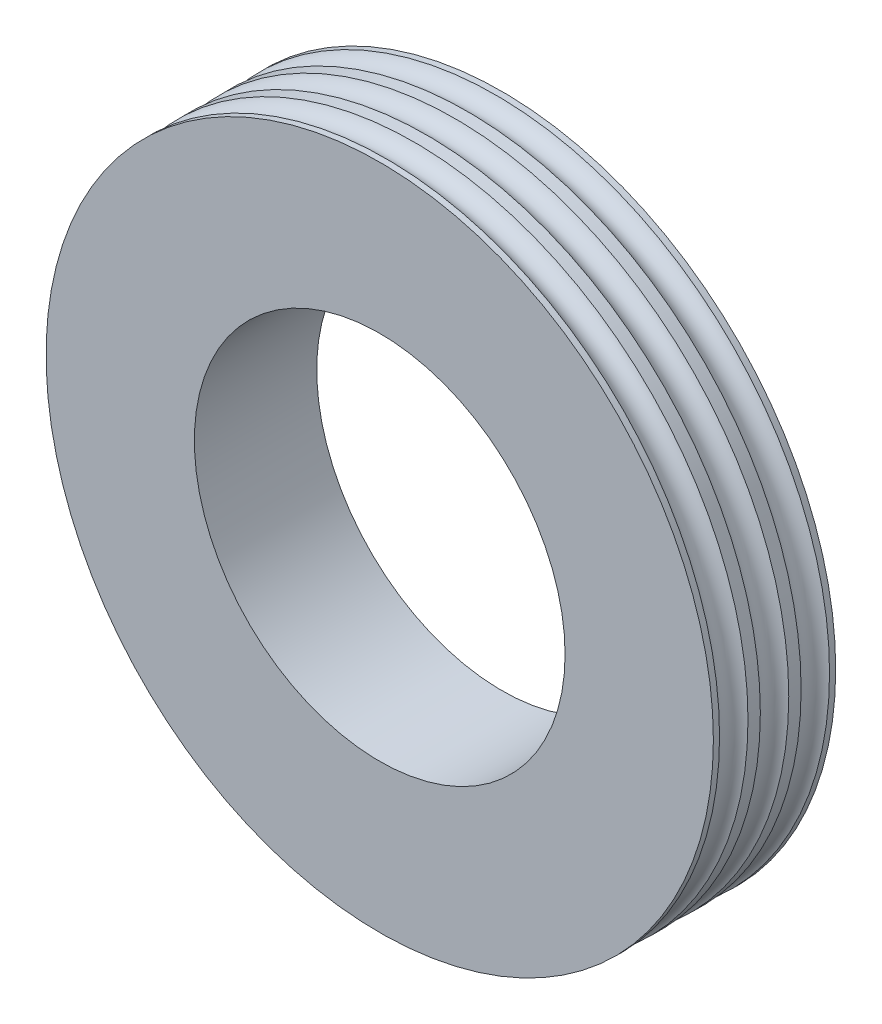
SolidWorks part; units mm, degrees
ref_plane "Front Plane" through (0, 0, 0) normal (0, 0, 1) x (1, 0, 0)
ref_plane "Top Plane" through (0, 0, 0) normal (0, 1, 0) x (1, 0, 0)
ref_plane "Right Plane" through (0, 0, 0) normal (1, 0, 0) x (0, 0, -1)
sketch "Sketch2" plane through (0, 0, 0) normal (1, 0, 0) x (0, 0, -1)
  line L0 (-0.34, 3) -> (-0.34, 5.4)
  line L1 (-0.34, 5.4) -> (-0.44, 5.4)
  line L2 (-1, 5.4) -> (-1, 3)
  line L4 (-1, 3) -> (-0.34, 3)
  line L5 (-3.0147, 0) -> (3.0268, 0) construction
  line L6 (-0.9, 5.4) -> (-1, 5.4)
  arc A0 (-0.9, 5.4) -> (-0.44, 5.4) centre (-0.67, 5.5) ccw
  dimension "D6" = 0.1
  dimension "D1" = 3
  dimension "D2" = 0.66
  dimension "D3" = 5.4
  dimension "D4" = 0.1
  dimension "D5" = 0.1
revolve "Revolve1" add sketch "Sketch2" angle 360 about L5
ref_plane "Plane1" through (0, 0, 0.34) normal (0, 0, -1) x (-1, 0, 0)
mirror "Mirror2" about plane through (0, 0, 0.34) normal (0, 0, -1) of "Revolve1"
ref_plane "Plane3" through (0, 0, 1) normal (0, 0, 1) x (1, 0, 0)
mirror "Mirror3" about plane through (0, 0, 1) normal (0, 0, 1) of "Revolve1"
